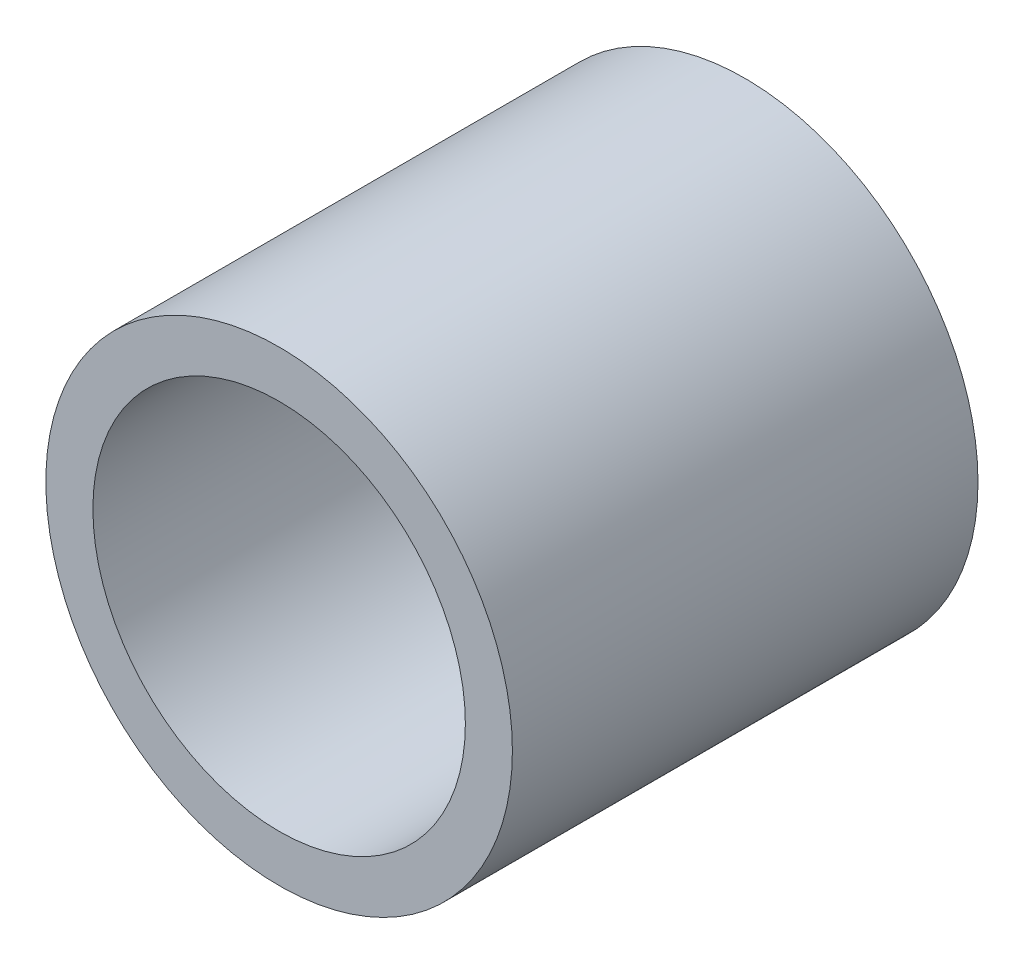
SolidWorks part; units mm, degrees
ref_plane "Front" through (0, 0, 0) normal (0, 0, 1) x (1, 0, 0)
ref_plane "Top" through (0, 0, 0) normal (0, 1, 0) x (1, 0, 0)
ref_plane "Right" through (0, 0, 0) normal (1, 0, 0) x (0, 0, -1)
sketch "Sketch1" plane through (0, 0, 0) normal (0, 0, 1) x (1, 0, 0)
  circle A0 centre (0, 0) radius 7.954
  circle A1 centre (0, 0) radius 6.35
  dimension "D1" = 12.7
  dimension "D2" = 15.908
extrude "Boss-Extrude1" add sketch "Sketch1" along normal blind 15.875
